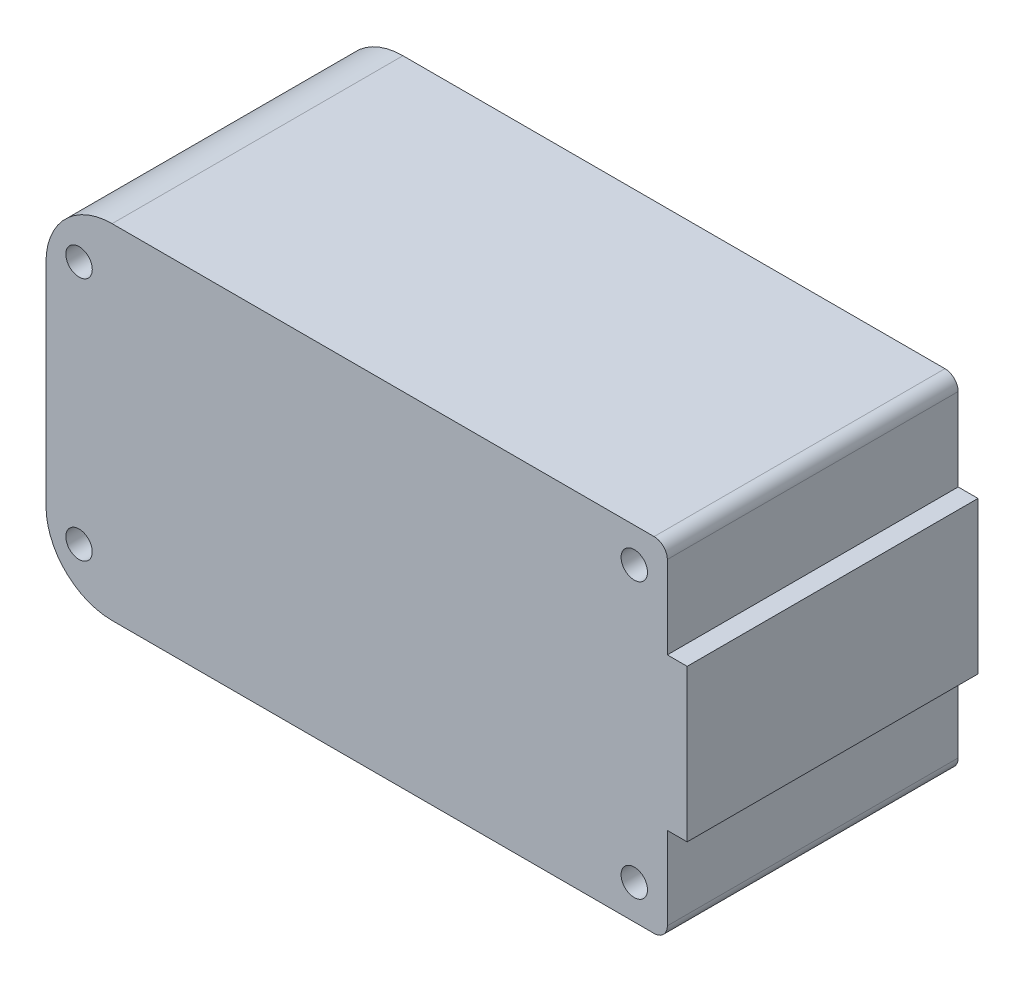
SolidWorks part; units mm, degrees
ref_plane "Front" through (0, 0, 0) normal (0, 0, 1) x (1, 0, 0)
ref_plane "Top" through (0, 0, 0) normal (0, 1, 0) x (1, 0, 0)
ref_plane "Right" through (0, 0, 0) normal (1, 0, 0) x (0, 0, -1)
sketch "Sketch1" plane through (0, 0, 0) normal (0, 0, 1) x (1, 0, 0)
  line L0 (12, 0) -> (37, 0) construction
  line L1 (35.5, -13) -> (-11.5, -13)
  line L2 (35.5, -13) -> (35.5, -5.75)
  line L3 (35.5, 13) -> (-11.5, 13)
  line L4 (-11.5, -13) -> (-11.5, 13)
  line L5 (35.5, -13) -> (-11.5, 13) construction
  line L6 (35.5, 13) -> (-11.5, -13) construction
  line L10 (35.5, 5.75) -> (35.5, 13)
  line L11 (35.5, 5.75) -> (37, 5.75)
  line L12 (35.5, -5.75) -> (37, -5.75)
  line L13 (37, 5.75) -> (37, -5.75)
  circle A0 centre (-9, 9.25) radius 1
  circle A1 centre (33, 10.4) radius 1
  circle A2 centre (33, -10.4) radius 1
  circle A3 centre (-9, -9.25) radius 1
  point P0 (12, 0)
  dimension "D6" = 2
  dimension "D7" = 20.8
  dimension "D8" = 2.5
  dimension "D9" = 18.5
  dimension "D10" = 2.5
  dimension "D1" = 47
  dimension "D2" = 26
  dimension "D3" = 11.5
  dimension "D4" = 11.5
  dimension "D5" = 1.5
extrude "Boss-Extrude1" add sketch "Sketch1" along normal mid plane 22
fillet "Fillet1" radius 5 2 edges at (-11.5, 13, 0) (-11.5, -13, 0)
fillet "Fillet2" radius 1 2 edges at (35.5, 13, 0) (35.5, -13, 0)
